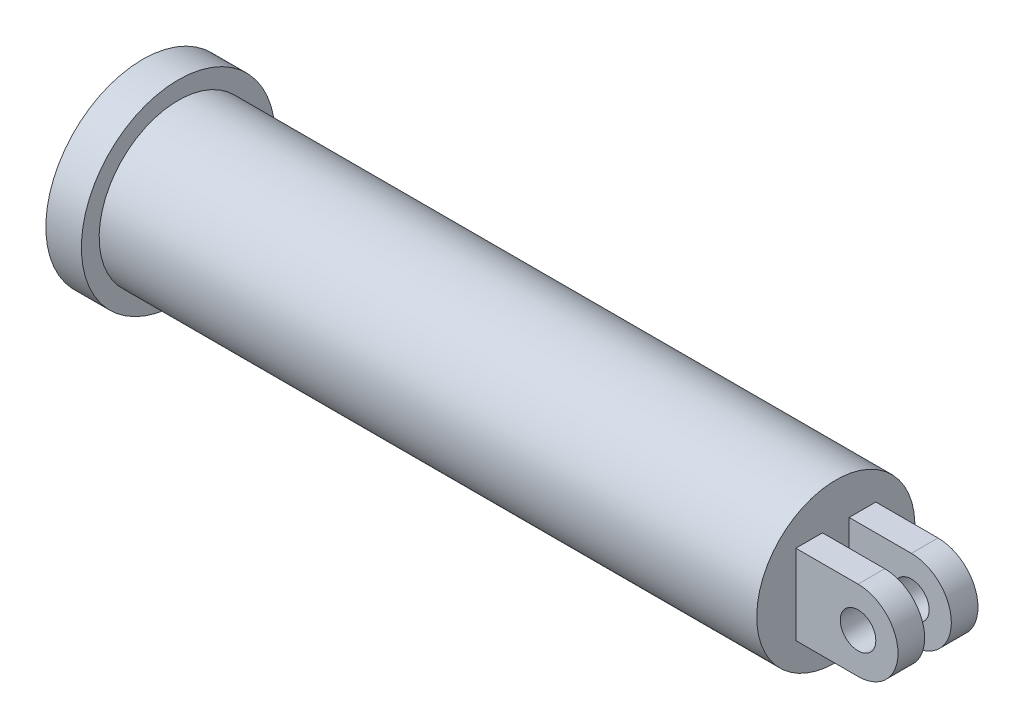
SolidWorks part; units mm, degrees
ref_plane "Front Plane" through (0, 0, 0) normal (0, 0, 1) x (1, 0, 0)
ref_plane "Top Plane" through (0, 0, 0) normal (0, 1, 0) x (1, 0, 0)
ref_plane "Right Plane" through (0, 0, 0) normal (1, 0, 0) x (0, 0, -1)
sketch "Sketch2" plane through (0, 0, 0) normal (0, 0, 1) x (1, 0, 0)
  line L0 (-195, 0) -> (195, 0)
  line L1 (195, 0) -> (195, 44.5)
  line L2 (195, 44.5) -> (-175, 44.5)
  line L3 (-175, 44.5) -> (-175, 54.5)
  line L4 (-175, 54.5) -> (-195, 54.5)
  line L5 (-195, 54.5) -> (-195, 0)
  point P3 (0, 0)
  dimension "D1" = 44.5
  dimension "D2" = 54.5
  dimension "D3" = 20
  dimension "D4" = 390
revolve "Revolve1" add sketch "Sketch2" angle 360 about L0
ref_plane "Plane1" through (0, 0, 7.5) normal (0, 0, 1) x (1, 0, 0)
sketch "Sketch3" plane through (0, 0, 7.5) normal (0, 0, 1) x (1, 0, 0)
  line L0 (195, 22.5) -> (230, 22.5)
  line L1 (195, -44.5) -> (195, 44.5) construction
  line L2 (195, -22.5) -> (230, -22.5)
  line L3 (230, 22.5) -> (230, -22.5) construction
  line L4 (195, 22.5) -> (195, -22.5)
  arc A0 (230, 22.5) -> (230, -22.5) centre (230, 0) cw
  circle A1 centre (230, 0) radius 10
  point P7 (195, 0)
  dimension "D3" = 20
  dimension "D4" = 22.5
  dimension "D1" = 45
  dimension "D2" = 35
extrude "Boss-Extrude1" add sketch "Sketch3" along normal blind 15
mirror "Mirror1" about plane through (0, 0, 0) normal (0, 0, 1) of "Boss-Extrude1"
